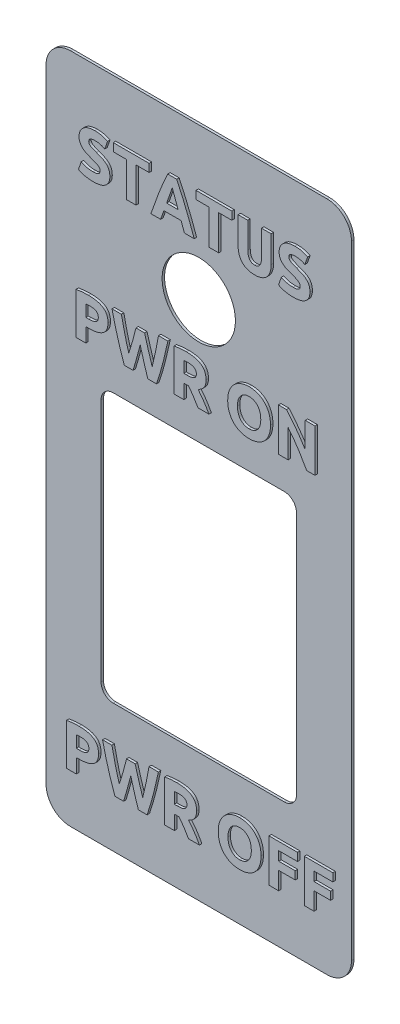
SolidWorks part; units mm, degrees
ref_plane "Front Plane" through (0, 0, 0) normal (0, 0, 1) x (1, 0, 0)
ref_plane "Top Plane" through (0, 0, 0) normal (0, 1, 0) x (1, 0, 0)
ref_plane "Right Plane" through (0, 0, 0) normal (1, 0, 0) x (0, 0, -1)
sketch "Sketch1" plane through (0, 0, 0) normal (0, 0, 1) x (1, 0, 0)
  line L1 (0, 0) -> (25, 0)
  line L2 (0, 0) -> (0, 55)
  line L3 (0, 55) -> (25, 55)
  line L4 (25, 0) -> (25, 55)
  dimension "D1" = 25
  dimension "D2" = 55
extrude "Body" add sketch "Sketch1" along normal blind 0.2
sketch "Sketch3" plane through (0, 0, 0.2) normal (0, 0, 1) x (1, 0, 0)
  line L0 (0, 0) -> (25, 0) construction
  line L1 (4.5, 32.5) -> (20.5, 32.5)
  line L2 (4.5, 32.5) -> (4.5, 10.5)
  line L3 (4.5, 10.5) -> (20.5, 10.5)
  line L4 (20.5, 32.5) -> (20.5, 10.5)
  circle A0 centre (12.5, 42.6) radius 3
  point P7 (12.5, 32.5)
  point P10 (12.5, 10.5)
  point P13 (12.5, 0)
  dimension "D3" = 6
  dimension "D1" = 16
  dimension "D2" = 22
  dimension "D4" = 10.1
  dimension "D5" = 10.5
extrude "Cuts" cut sketch "Sketch3" against normal through all
sketch "Sketch2" plane through (0, 0, 0.2) normal (0, 0, 1) x (1, 0, 0)
  text T0 "PWR ON" font "Ubuntu" height 3.5
  text T1 "PWR OFF" font "Ubuntu" height 3.5
  text T2 "STATUS" font "Ubuntu" height 3.5
extrude "Text" add sketch "Sketch2" along normal blind 0.2
fillet "InsideFillet" radius 1 4 edges at (4.5, 10.5, 0.1) (20.5, 10.5, 0.1) (20.5, 32.5, 0.1) (4.5, 32.5, 0.1)
fillet "OutsideFillet" radius 2 4 edges at (0, 0, 0.1) (25, 0, 0.1) (0, 55, 0.1) (25, 55, 0.1)
